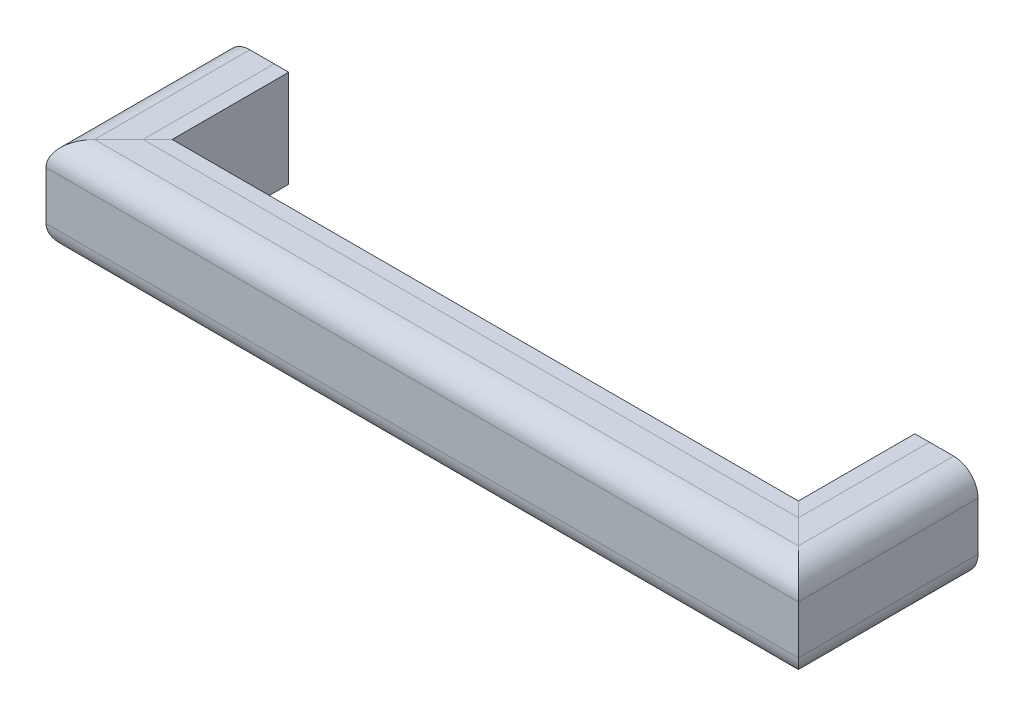
SolidWorks part; units mm, degrees
ref_plane "Front" through (0, 0, 0) normal (0, 0, 1) x (1, 0, 0)
ref_plane "Top" through (0, 0, 0) normal (0, 1, 0) x (1, 0, 0)
ref_plane "Right" through (0, 0, 0) normal (1, 0, 0) x (0, 0, -1)
sketch "Sketch1" plane through (0, 0, 0) normal (0, 0, 1) x (1, 0, 0)
  line L0 (-409.575, 0) -> (409.575, 0) construction
  line L1 (-428.625, 127) -> (-460.375, 127)
  line L2 (-409.575, 0) -> (-428.625, 0)
  line L3 (-409.575, 0) -> (-409.575, 127)
  line L4 (-409.575, 127) -> (-428.625, 127)
  line L5 (-428.625, 0) -> (-428.625, 127) construction
  line L6 (-492.125, 95.25) -> (-492.125, 31.75)
  line L7 (-460.375, 0) -> (-428.625, 0)
  circle A0 centre (-460.375, 95.25) radius 31.75 construction
  circle A1 centre (-460.375, 31.75) radius 31.75 construction
  arc A2 (-460.375, 127) -> (-492.125, 95.25) centre (-460.375, 95.25) ccw
  arc A3 (-492.125, 31.75) -> (-460.375, 0) centre (-460.375, 31.75) ccw
  dimension "D2" = 19.05
  dimension "D3" = 63.5
  dimension "D1" = 819.15
sketch "Sketch2" plane through (0, 0, 0) normal (0, 1, 0) x (1, 0, 0)
  line L0 (-409.575, 0) -> (-409.575, -152.4)
  line L1 (-409.575, 0) -> (409.575, 0) construction
  line L2 (-409.575, -152.4) -> (409.575, -152.4)
  line L3 (409.575, -152.4) -> (409.575, 0)
  dimension "D1" = 152.4
sweep "Sweep1" add profiles "Sketch1" path "Sketch2"
